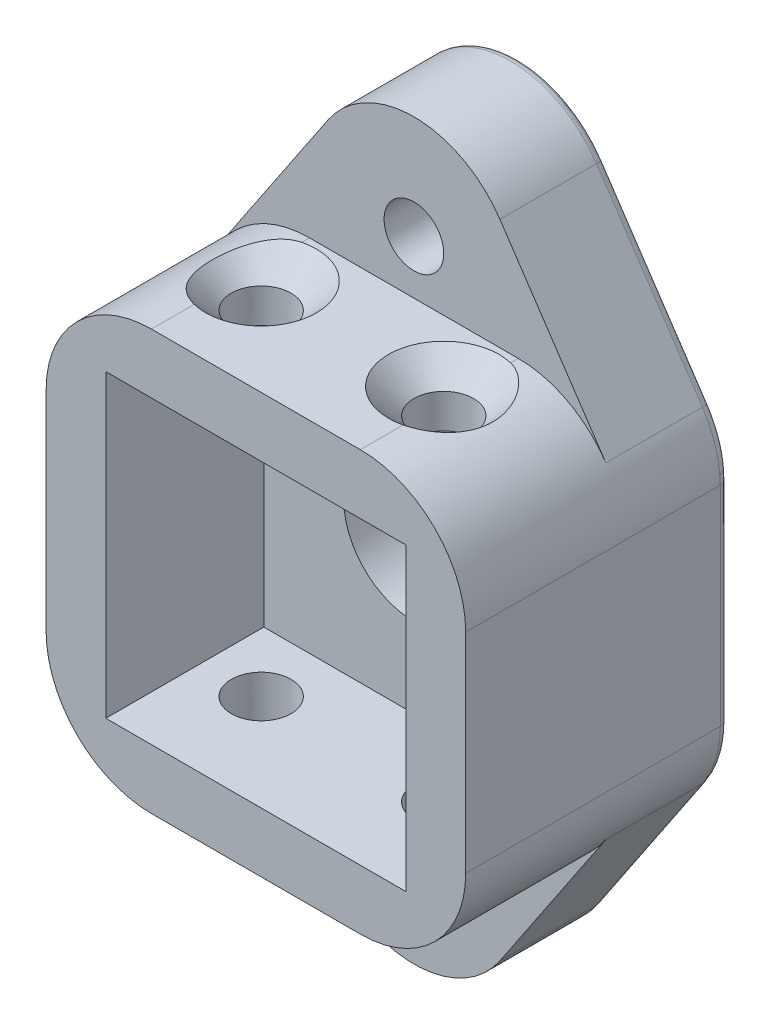
SolidWorks part; units mm, degrees
ref_plane "Plan de face" through (0, 0, 0) normal (0, 0, 1) x (1, 0, 0)
ref_plane "Plan de dessus" through (0, 0, 0) normal (0, 1, 0) x (1, 0, 0)
ref_plane "Plan de droite" through (0, 0, 0) normal (1, 0, 0) x (0, 0, -1)
sketch "Sketch1" plane through (0, 0, 0) normal (0, 0, 1) x (1, 0, 0)
  line L1 (-11.95, -11.95) -> (11.95, -11.95)
  line L2 (-11.95, -11.95) -> (-11.95, 11.95)
  line L3 (-11.95, 11.95) -> (11.95, 11.95)
  line L4 (11.95, -11.95) -> (11.95, 11.95)
  line L5 (-11.95, -11.95) -> (11.95, 11.95) construction
  line L6 (-11.95, 11.95) -> (11.95, -11.95) construction
  line L7 (-8.55, -8.55) -> (8.55, -8.55)
  line L8 (-8.55, -8.55) -> (-8.55, 8.55)
  line L9 (-8.55, 8.55) -> (8.55, 8.55)
  line L10 (8.55, -8.55) -> (8.55, 8.55)
  line L11 (-8.55, -8.55) -> (8.55, 8.55) construction
  line L12 (-8.55, 8.55) -> (8.55, -8.55) construction
  point P0 (0, 0)
  point P5 (0, 0)
  dimension "D1" = 23.9
  dimension "D2" = 23.9
  dimension "D3" = 17.1
  dimension "D4" = 17.1
extrude "Boss-Extrude1" add sketch "Sketch1" along normal blind 15
fillet "Fillet1" radius 6 4 edges at (-11.95, -11.95, 7.5) (11.95, -11.95, 7.5) (11.95, 11.95, 7.5) (-11.95, 11.95, 7.5)
sketch "Sketch3" plane through (0, 0, 0) normal (0, 0, -1) x (-1, 0, 0)
  line L4 (-5.95, -11.95) -> (5.95, -11.95)
  line L5 (11.95, -5.95) -> (11.95, 5.95)
  line L6 (5.95, 11.95) -> (-5.95, 11.95)
  line L7 (-11.95, 5.95) -> (-11.95, -5.95)
  line L8 (-5.95, -11.95) -> (5.95, -11.95)
  line L9 (11.95, -5.95) -> (11.95, 5.95)
  line L10 (5.95, 11.95) -> (-5.95, 11.95)
  line L11 (-11.95, 5.95) -> (-11.95, -5.95)
  circle A0 centre (0, 0) radius 4
  arc A4 (5.95, -11.95) -> (11.95, -5.95) centre (5.95, -5.95) ccw
  arc A5 (11.95, 5.95) -> (5.95, 11.95) centre (5.95, 5.95) ccw
  arc A6 (-5.95, 11.95) -> (-11.95, 5.95) centre (-5.95, 5.95) ccw
  arc A7 (-11.95, -5.95) -> (-5.95, -11.95) centre (-5.95, -5.95) ccw
  arc A8 (5.95, -11.95) -> (11.95, -5.95) centre (5.95, -5.95) ccw
  arc A9 (11.95, 5.95) -> (5.95, 11.95) centre (5.95, 5.95) ccw
  arc A10 (-5.95, 11.95) -> (-11.95, 5.95) centre (-5.95, 5.95) ccw
  arc A11 (-11.95, -5.95) -> (-5.95, -11.95) centre (-5.95, -5.95) ccw
  dimension "D2" = 8
  dimension "D1" = 0
extrude "Boss-Extrude2" add sketch "Sketch3" against normal blind 6
sketch "Sketch2" plane through (0, 0, 0) normal (0, 0, -1) x (-1, 0, 0)
  line L0 (0, 15) -> (0, 11.95) construction
  line L3 (-5.95, 11.95) -> (5.95, 11.95) construction
  line L8 (5.9001, 11.95) -> (-5.9, 11.95)
  line L10 (10.9329, 9.2923) -> (4.8998, 18.2866)
  line L11 (-4.8998, 18.2866) -> (-10.9329, 9.2923)
  line L12 (0, 0) -> (2.476, 0) construction
  line L13 (0, -15) -> (0, -11.95) construction
  line L14 (-4.8998, -18.2866) -> (-10.9329, -9.2923)
  line L16 (10.9329, -9.2923) -> (4.8998, -18.2866)
  line L17 (5.9001, -11.95) -> (-5.9, -11.95)
  arc A0 (4.8998, 18.2866) -> (-4.8998, 18.2866) centre (0, 15) ccw
  arc A4 (11.95, 5.95) -> (5.95, 11.95) centre (5.95, 5.95) ccw construction
  arc A5 (10.9329, 9.2923) -> (5.95, 11.95) centre (5.95, 5.95) ccw
  arc A6 (-5.95, 11.95) -> (-11.95, 5.95) centre (-5.95, 5.95) ccw construction
  arc A7 (-5.95, 11.95) -> (-10.9329, 9.2923) centre (-5.95, 5.95) ccw
  arc A8 (-5.95, -11.95) -> (-10.9329, -9.2923) centre (-5.95, -5.95) cw
  arc A9 (10.9329, -9.2923) -> (5.95, -11.95) centre (5.95, -5.95) cw
  arc A10 (4.8998, -18.2866) -> (-4.8998, -18.2866) centre (0, -15) cw
  dimension "D1" = 5.9
  dimension "D2" = 3.05
extrude "Boss-Extrude3" add sketch "Sketch2" against normal blind 6
hole_wizard "CBORE for M3 Hex Socket Head Cap Screw1" positions "Sketch4" profile "Sketch5" counterbore size "M3" standard "ISO" end condition through all
sketch "Sketch4" plane through (0, 0, 0) normal (0, 0, -1) x (-1, 0, 0)
  point P0 (0, 15)
  point P3 (0, -15)
sketch "Sketch5" plane through (0, 15, 0) normal (1, 0, 0) x (0, 1, 0)
  line L0 (0, 0) -> (0, 15)
  line L1 (0, 15) -> (1.7, 15)
  line L3 (1.7, 15) -> (1.7, 3.4)
  line L4 (1.7, 3.4) -> (3.25, 3.4)
  line L5 (3.25, 3.4) -> (3.25, 0)
  line L7 (3.25, 0) -> (0, 0)
  line L11 (0, -6.35) -> (0, 107.95) construction
  dimension "Thru Hole Dia." = 3.4
  dimension "Thru Hole Depth" = 15
  dimension "C'Bore Dia." = 6.5
  dimension "C'Bore Depth" = 3.4
fillet "Fillet2" radius 0.5 12 edges at (11.6901, 7.6968, 0) (11.95, 0, 0) (-11.6901, 7.6968, 0) (-11.6901, -7.6968, 0) (11.6901, -7.6968, 0) (-11.95, 0, 0) (7.9163, 13.7895, 0) (0, 20.9, 0) (-7.9163, 13.7895, 0) (7.9163, -13.7895, 0) (0, -20.9, 0) (-7.9163, -13.7895, 0)
hole_wizard "CSK for M3 Countersunk Flat Head Screw1" positions "Sketch7" profile "Sketch9" countersink size "M3" standard "ISO" end condition through all
sketch "Sketch7" plane through (0, 11.95, 0) normal (0, 1, 0) x (1, 0, 0)
  line L0 (4.4846, 0) -> (-4.4846, 0) construction
  point P0 (-5.2, -9.5)
  point P2 (5.2, -9.5)
  dimension "D1" = 10.4
  dimension "D2" = 5.2
  dimension "D3" = 9.5
sketch "Sketch9" plane through (-5.2, 11.95, 9.5) normal (1, 0, 0) x (0, 0, 1)
  line L0 (0, 0) -> (0, 32.85)
  line L1 (0, 32.85) -> (1.7, 32.85)
  line L2 (1.7, 32.85) -> (1.7, 1.45)
  line L3 (1.7, 1.45) -> (3.15, 0)
  line L5 (3.15, 0) -> (0, 0)
  line L6 (-1.7, 1.45) -> (-3.15, 0) construction
  line L11 (0, -6.35) -> (0, 107.95) construction
  dimension "Thru Hole Dia." = 3.4
  dimension "Thru Hole Depth" = 32.85
  dimension "Near C'Sink Dia." = 6.3
  dimension "Near C'Sink Angle" = 90
